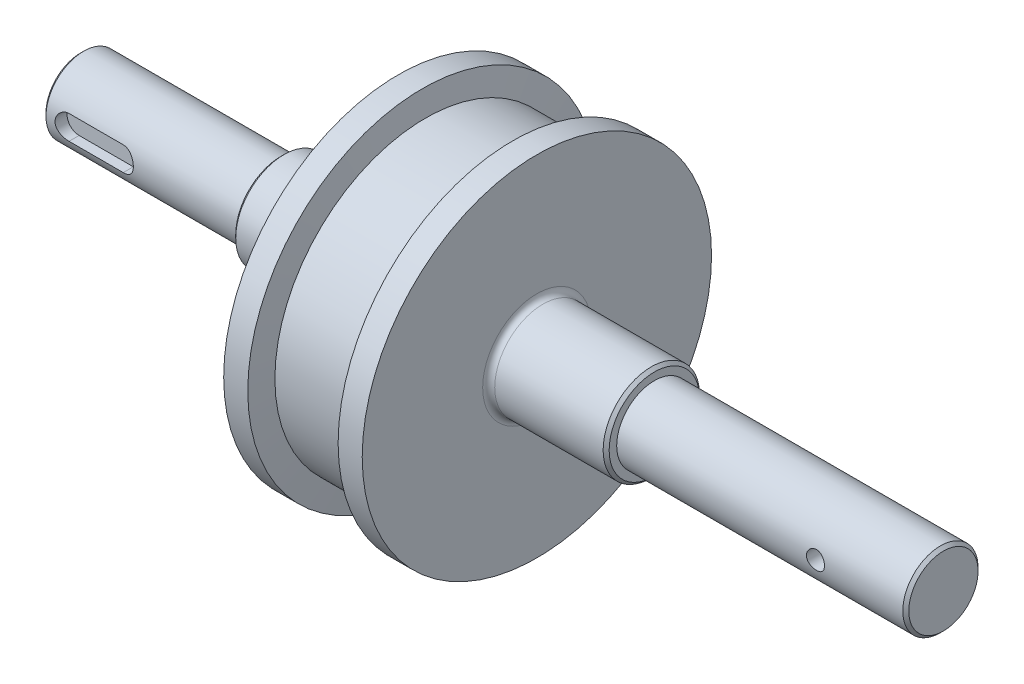
SolidWorks part; units mm, degrees
material "AISI 1045 钢，冷拔"
ref_plane "前视基准面" through (0, 0, 0) normal (0, 0, 1) x (1, 0, 0)
ref_plane "上视基准面" through (0, 0, 0) normal (0, 1, 0) x (1, 0, 0)
ref_plane "右视基准面" through (0, 0, 0) normal (1, 0, 0) x (0, 0, -1)
sketch "草图1" plane through (0, 0, 0) normal (0, 0, 1) x (1, 0, 0)
  line L0 (0, 0) -> (286.5, 0) construction
  line L1 (67.5, 16) -> (103.5, 16)
  line L2 (190.5, 15) -> (190.5, 12.5)
  line L3 (190.5, 12.5) -> (285.5, 12.5)
  line L4 (66.5, 15) -> (66.5, 12.5)
  line L5 (66.5, 12.5) -> (1, 12.5)
  line L6 (105.5, 18) -> (105.5, 58)
  line L7 (105.5, 58) -> (113.5, 58)
  line L8 (113.5, 58) -> (114.5, 50)
  line L9 (114.5, 50) -> (142.5, 50)
  line L10 (142.5, 50) -> (143.5, 58)
  line L11 (143.5, 58) -> (151.5, 58)
  line L12 (151.5, 58) -> (151.5, 18)
  line L13 (153.5, 16) -> (189.5, 16)
  line L14 (0, 0) -> (0, 11.5)
  line L15 (286.5, 0) -> (286.5, 11.5)
  line L16 (0, 11.5) -> (1, 12.5)
  line L17 (66.5, 15) -> (67.5, 16)
  line L18 (189.5, 16) -> (190.5, 15)
  line L19 (286.5, 11.5) -> (285.5, 12.5)
  line L20 (0, 0) -> (286.5, 0)
  arc A0 (151.5, 18) -> (153.5, 16) centre (153.5, 18) ccw
  arc A1 (105.5, 18) -> (103.5, 16) centre (103.5, 18) cw
  point P3 (66.5, 16)
  point P5 (190.5, 16)
  point P11 (286.5, 12.5)
  point P18 (0, 12.5)
  point P27 (151.5, 16)
  dimension "D16" = 2
  dimension "D1" = 124
  dimension "D2" = 8
  dimension "D3" = 8
  dimension "D4" = 50
  dimension "D5" = 28
  dimension "D6" = 8
  dimension "D7" = 8
  dimension "D8" = 9
  dimension "D9" = 9
  dimension "D10" = 39
  dimension "D11" = 12.5
  dimension "D12" = 12.5
  dimension "D13" = 16
  dimension "D14" = 66.5
  dimension "D15" = 286.5
revolve "旋转1" add sketch "草图1" angle 360 about L0
sketch "草图2" plane through (0, 0, 0) normal (0, 0, 1) x (1, 0, 0)
  line L0 (286.5, -11.5) -> (286.5, 11.5) construction
  circle A0 centre (256.5, 0) radius 3
  dimension "D1" = 30
  dimension "D2" = 6
extrude "切除-拉伸1" cut sketch "草图2" against normal mid plane 30 contours A0
ref_plane "基准面1" through (0, 0, 12.5) normal (0, 0, 1) x (1, 0, 0)
sketch "草图3" plane through (0, 0, 12.5) normal (0, 0, 1) x (1, 0, 0)
  line L0 (0, 0) -> (52.4804, 0) construction
  line L1 (8, 4) -> (26, 4)
  line L3 (8, -4) -> (26, -4)
  arc A0 (8, 4) -> (8, -4) centre (8, 0) ccw
  arc A1 (26, -4) -> (26, 4) centre (26, 0) ccw
  dimension "D2" = 4
  dimension "D3" = 4
  dimension "D4" = 8
  dimension "D1" = 8
  dimension "D5" = 18
extrude "切除-拉伸2" cut sketch "草图3" against normal blind 4
